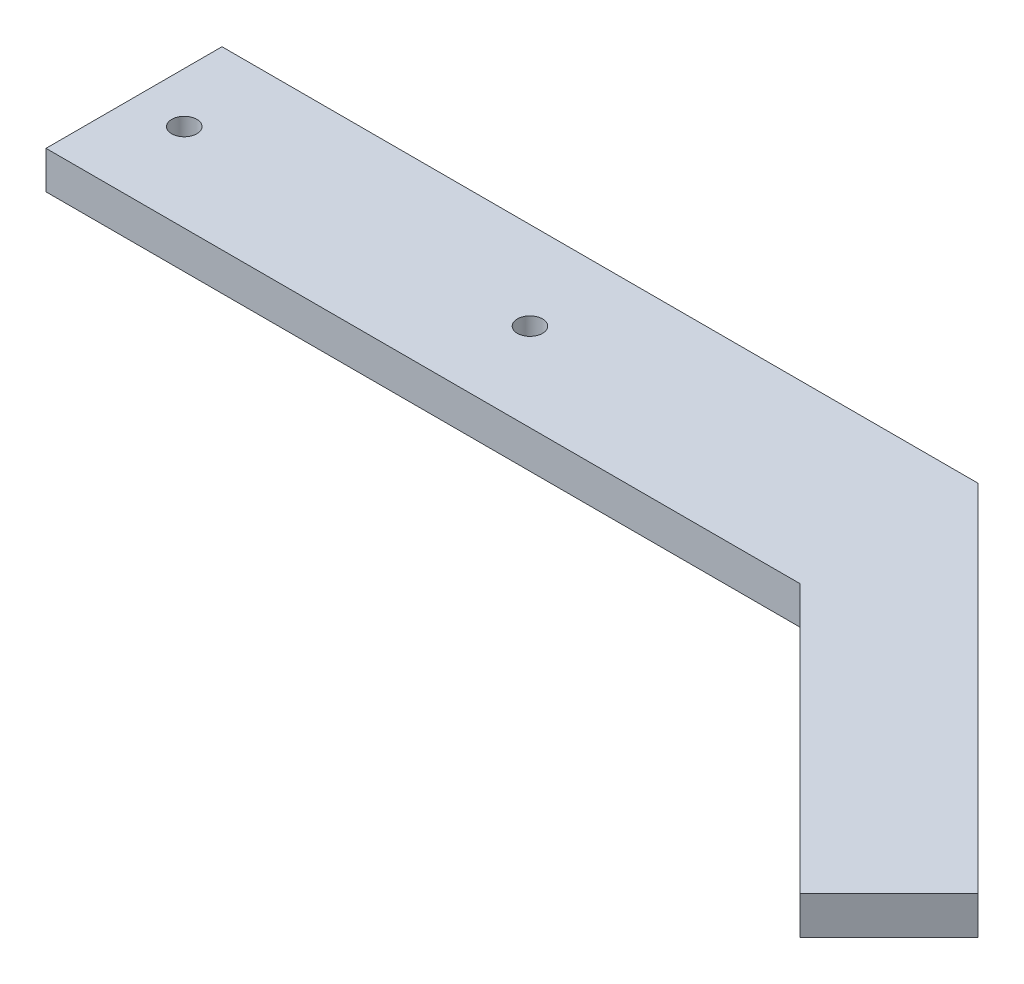
SolidWorks part; units mm, degrees
ref_plane "Front Plane" through (0, 0, 0) normal (0, 0, 1) x (1, 0, 0)
ref_plane "Top Plane" through (0, 0, 0) normal (0, 1, 0) x (1, 0, 0)
ref_plane "Right Plane" through (0, 0, 0) normal (1, 0, 0) x (0, 0, -1)
sketch "Sketch1" plane through (0, 0, 0) normal (0, 1, 0) x (1, 0, 0)
  line L0 (81.3553, -21.3553) -> (60, 0)
  line L1 (0, 0) -> (60, 0)
  line L2 (0, 0) -> (0, 14)
  line L3 (0, 14) -> (60.1421, 14)
  line L4 (81.3553, -21.3553) -> (88.4264, -14.2843)
  line L5 (60.1421, 14) -> (88.4264, -14.2843)
  point P1 (0, 0)
  dimension "D1" = 45
  dimension "D2" = 60
  dimension "D3" = 14
  dimension "D4" = 40
  dimension "D5" = 10
extrude "Boss-Extrude1" add sketch "Sketch1" along normal blind 3
sketch "Sketch2" plane through (0, 3, 0) normal (0, 1, 0) x (1, 0, 0)
  line L0 (0, 0) -> (60, 0) construction
  line L1 (60.1421, 14) -> (0, 14) construction
  line L2 (0, 14) -> (0, 0) construction
  circle A0 centre (4, 7) radius 1
  circle A1 centre (31.5, 7) radius 1
  dimension "D1" = 2
  dimension "D2" = 2
  dimension "D3" = 7
  dimension "D4" = 7
  dimension "D5" = 4
  dimension "D6" = 27.5
extrude "Cut-Extrude1" cut sketch "Sketch2" against normal up to surface (3 mm away) up to face at (48.3206, 0, 1.2733)
